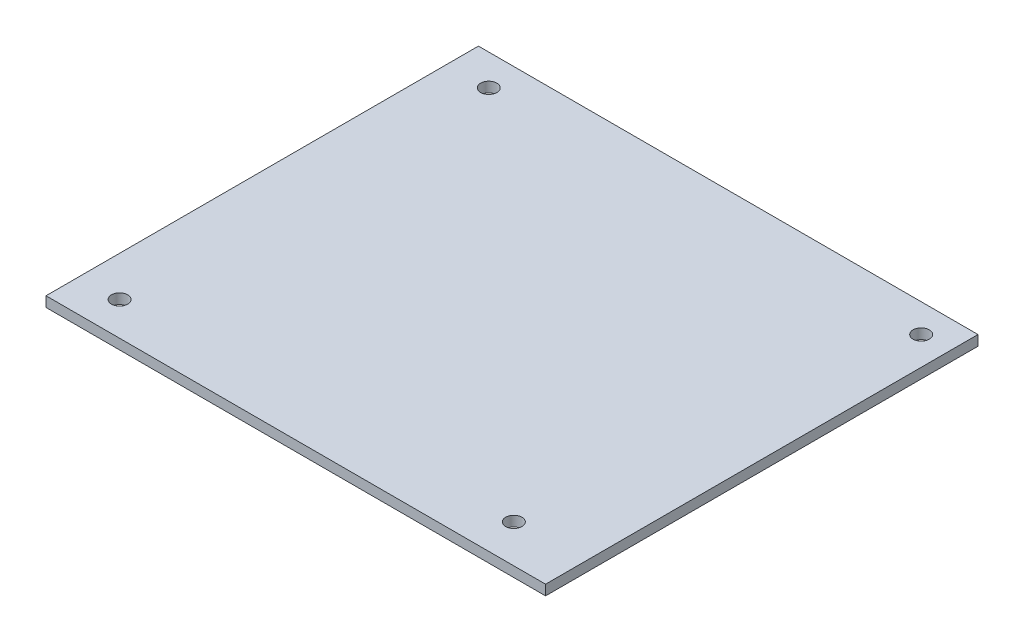
SolidWorks part; units mm, degrees
ref_plane "Front Plane" through (0, 0, 0) normal (0, 0, 1) x (1, 0, 0)
ref_plane "Top Plane" through (0, 0, 0) normal (0, 1, 0) x (1, 0, 0)
ref_plane "Right Plane" through (0, 0, 0) normal (1, 0, 0) x (0, 0, -1)
sketch "Sketch1" plane through (0, 0, 0) normal (0, 1, 0) x (1, 0, 0)
  line L1 (-49.149, -42.545) -> (49.149, -42.545)
  line L2 (-49.149, -42.545) -> (-49.149, 42.545)
  line L3 (-49.149, 42.545) -> (49.149, 42.545)
  line L4 (49.149, -42.545) -> (49.149, 42.545)
  line L5 (-49.149, -42.545) -> (49.149, 42.545) construction
  line L6 (-49.149, 42.545) -> (49.149, -42.545) construction
  circle A0 centre (-41.021, 36.449) radius 1.6
  circle A1 centre (43.561, 36.957) radius 1.6
  circle A2 centre (35.4146, -35.0573) radius 1.6
  circle A3 centre (-41.275, -35.941) radius 1.6
  point P0 (0, 0)
  point P16 (-41.2891, -37.4834)
  dimension "D3" = 3.2
  dimension "D4" = 5.588
  dimension "D1" = 98.298
  dimension "D2" = 85.09
  dimension "D5" = 5.588
  dimension "D6" = 6.096
  dimension "D7" = 8.128
  dimension "D8" = 7.874
  dimension "D9" = 6.604
extrude "Boss-Extrude1" add sketch "Sketch1" along normal blind 2
